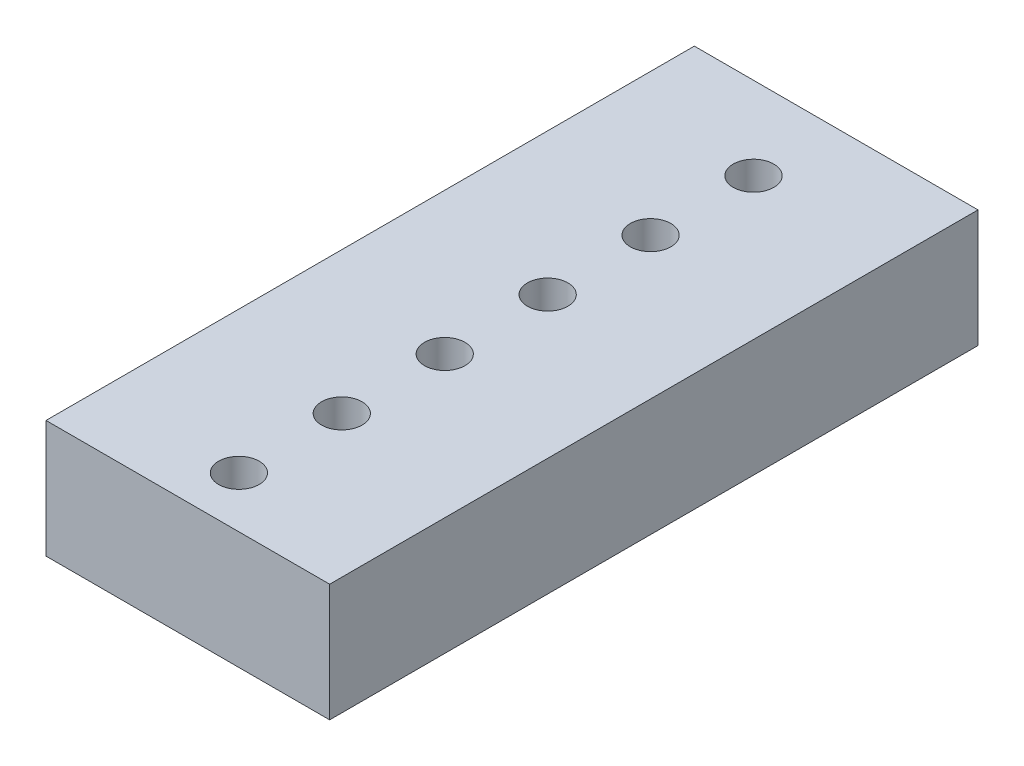
SolidWorks part; units mm, degrees
ref_plane "Front Plane" through (0, 0, 0) normal (0, 0, 1) x (1, 0, 0)
ref_plane "Top Plane" through (0, 0, 0) normal (0, 1, 0) x (1, 0, 0)
ref_plane "Right Plane" through (0, 0, 0) normal (1, 0, 0) x (0, 0, -1)
sketch "Sketch1" plane through (0, 0, 0) normal (0, 1, 0) x (1, 0, 0)
  line L1 (3.5, 8) -> (-3.5, 8)
  line L2 (3.5, 8) -> (3.5, -8)
  line L3 (3.5, -8) -> (-3.5, -8)
  line L4 (-3.5, 8) -> (-3.5, -8)
  line L5 (3.5, 8) -> (-3.5, -8) construction
  line L6 (3.5, -8) -> (-3.5, 8) construction
  line L7 (-0.96, 13.19) -> (1.58, 13.19) construction
  circle A0 centre (0, 13.19) radius 0.5
  circle A1 centre (1.58, 13.19) radius 0.5 construction
  point P0 (0, 0)
  point P13 (0, 8)
  dimension "D1" = 7
  dimension "D2" = 16
extrude "Boss-Extrude1" add sketch "Sketch1" along normal mid plane 2.9
sketch "Sketch2" plane through (0, 1.45, 0) normal (0, 1, 0) x (1, 0, 0)
  line L0 (3.5, 8) -> (-3.5, 8) construction
  circle A0 centre (0, 5.96) radius 0.5
  dimension "D1" = 1
  dimension "D2" = 2.04
extrude "Cut-Extrude1" cut sketch "Sketch2" against normal through all
pattern_linear "LPattern1" count 12 spacing 2.54 along (0, 0, 1) of "Cut-Extrude1"
